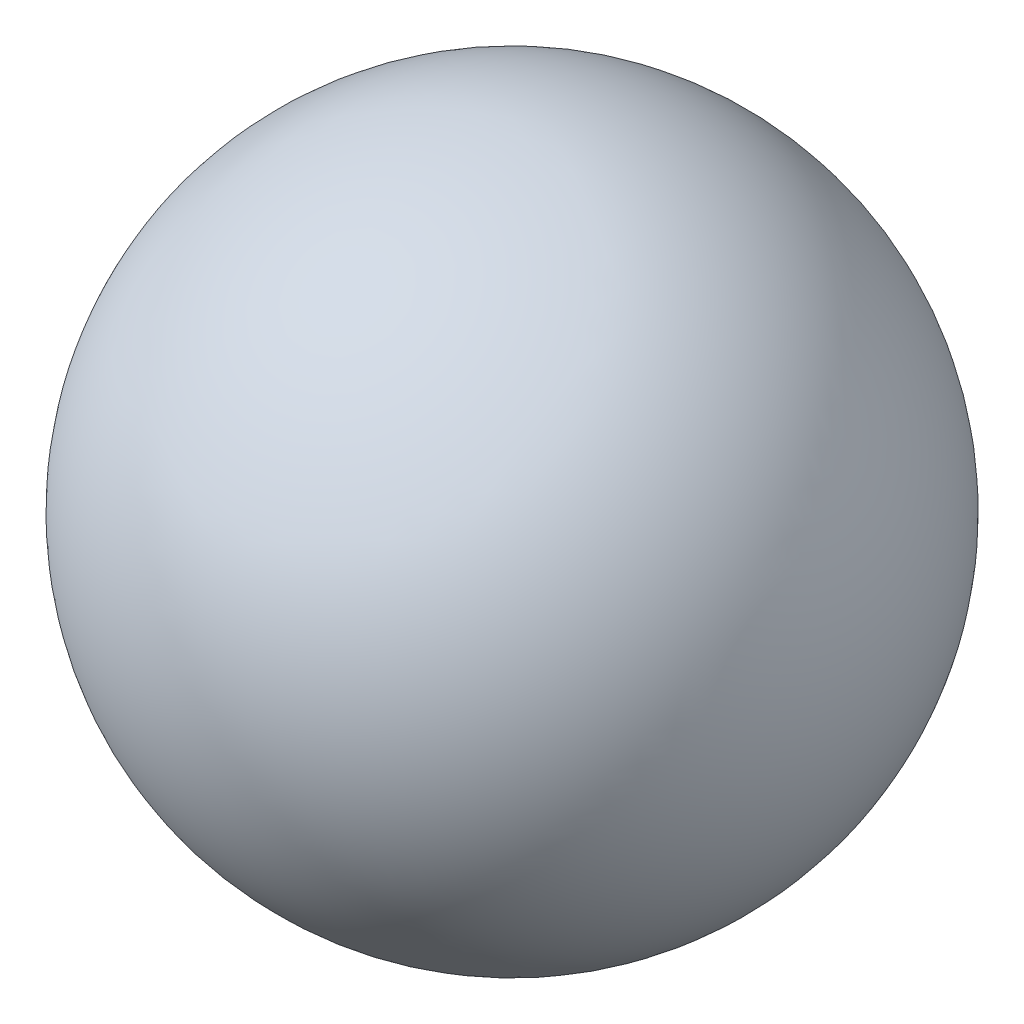
SolidWorks part; units mm, degrees
ref_plane "Front Plane" through (0, 0, 0) normal (0, 0, 1) x (1, 0, 0)
ref_plane "Top Plane" through (0, 0, 0) normal (0, 1, 0) x (1, 0, 0)
ref_plane "Right Plane" through (0, 0, 0) normal (1, 0, 0) x (0, 0, -1)
ref_plane "Plane1" through (0, 0, 0) normal (0, 0, 1) x (1, 0, 0)
sketch "Sketch1" plane through (0, 0, 0) normal (0, 0, 1) x (1, 0, 0)
  line L0 (3.492, 4.76) -> (1.508, 4.76)
  line L1 (3.492, 4.76) -> (1.508, 4.76) construction
  arc A0 (1.508, 4.76) -> (3.492, 4.76) centre (2.5, 4.76) cw
revolve "Revolve1" add sketch "Sketch1" angle 360 about L1
